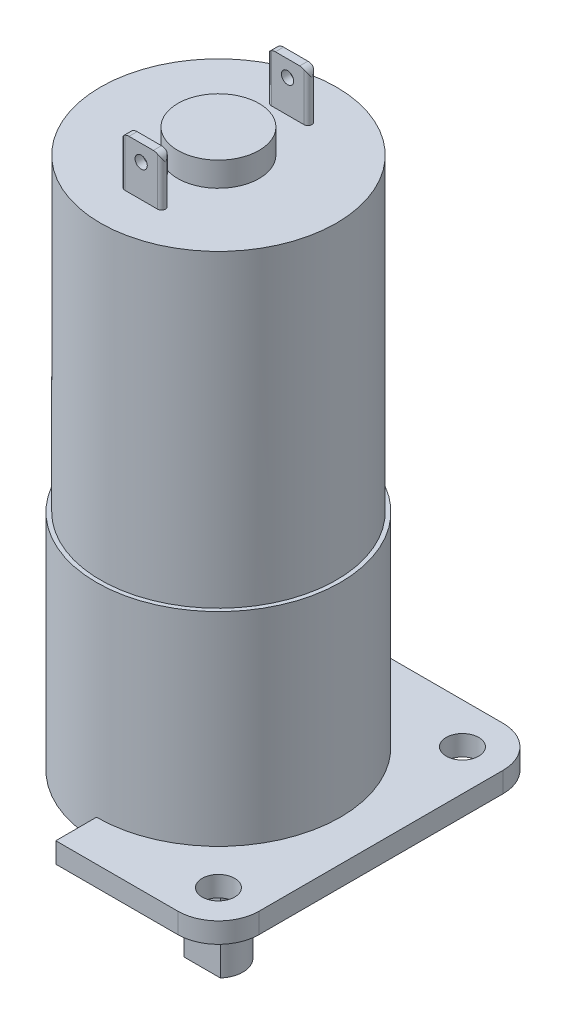
SolidWorks part; units mm, degrees
ref_plane "Alzado" through (0, 0, 0) normal (0, 0, 1) x (1, 0, 0)
ref_plane "Planta" through (0, 0, 0) normal (0, 1, 0) x (1, 0, 0)
ref_plane "Vista lateral" through (0, 0, 0) normal (1, 0, 0) x (0, 0, -1)
sketch "Croquis1" plane through (0, 0, 0) normal (0, 1, 0) x (1, 0, 0)
  circle A0 centre (0, 0) radius 14.5
  dimension "D1" = 29
extrude "Motor" add sketch "Croquis1" along normal blind 38
sketch "Croquis2" plane through (0, 38, 0) normal (0, 1, 0) x (1, 0, 0)
  circle A0 centre (0, 0) radius 5
  dimension "D1" = 10
extrude "Saliente posterior" add sketch "Croquis2" along normal blind 3
sketch "Croquis3" plane through (0, 38, 0) normal (0, 1, 0) x (1, 0, 0)
  line L0 (-11.3688, 9) -> (11.3688, 9) construction
  line L1 (-2, 9) -> (2, 9) construction
  line L2 (-2, 9.5) -> (2, 9.5)
  line L3 (-2, 8.5) -> (2, 8.5)
  line L4 (-14.5, 0) -> (14.5, 0) construction
  line L5 (-2, -9) -> (2, -9) construction
  line L6 (-2, -9.5) -> (2, -9.5)
  line L7 (-2, -8.5) -> (2, -8.5)
  circle A0 centre (0, 0) radius 14.5 construction
  arc A1 (-2, 9.5) -> (-2, 8.5) centre (-2, 9) ccw
  arc A2 (2, 8.5) -> (2, 9.5) centre (2, 9) ccw
  arc A3 (-2, -9.5) -> (-2, -8.5) centre (-2, -9) cw
  arc A4 (2, -8.5) -> (2, -9.5) centre (2, -9) cw
  point P7 (0, 9)
  point P17 (0, -9)
  dimension "D3" = 0.5
  dimension "D1" = 9
  dimension "D2" = 4
extrude "Bornes" add sketch "Croquis3" along normal blind 6
sketch "Croquis4" plane through (0, 0, 9.5) normal (0, 0, 1) x (1, 0, 0)
  line L0 (0, 44) -> (0, 38) construction
  line L1 (-2, 44) -> (2, 44) construction
  line L2 (-2, 38) -> (2, 38) construction
  line L3 (-2.5, 43) -> (2.5, 43) construction
  line L4 (-2.5, 44) -> (-2.5, 38) construction
  line L5 (2.5, 38) -> (2.5, 44) construction
  line L6 (-1.5, 44) -> (-1.5, 38) construction
  line L7 (14.5, 38) -> (-14.5, 38) construction
  line L8 (-2, 44) -> (-2.5, 44) construction
  line L9 (2.5, 43) -> (2.5, 44)
  line L10 (2.5, 44) -> (1.5, 44)
  line L11 (-2.5, 43) -> (-2.5, 44)
  line L12 (-2.5, 44) -> (-1.5, 44)
  arc A0 (-2.5, 43) -> (-1.5, 44) centre (-1.5, 43) cw
  arc A1 (2.5, 43) -> (1.5, 44) centre (1.5, 43) ccw
  circle A2 centre (0, 42) radius 0.75
  line M2 (2, 38) -> (2, 44)
  line M3 (2, 44) -> (-2, 44)
  line M4 (-2, 44) -> (-2, 38)
  dimension "D3" = 1.5
  dimension "D1" = 1
  dimension "D2" = 1
  dimension "D4" = 2
extrude "Agujero Bornes" cut sketch "Croquis4" against normal through all contours A2 | A1 L9 L10 M2 | A1 M2 M3 | L11 A0 L12 M4 | A0 M4 M3
sketch "Croquis5" plane through (0, 0, 0) normal (0, -1, 0) x (1, 0, 0)
  circle A0 centre (0, 0) radius 15
  dimension "D1" = 30
extrude "Caja reductora" add sketch "Croquis5" along normal blind 25
sketch "Croquis6" plane through (0, -25, 0) normal (0, -1, 0) x (1, 0, 0)
  line L1 (-15, 20) -> (15, 20)
  line L2 (-20, 15) -> (-20, -15)
  line L3 (-15, -20) -> (15, -20)
  line L4 (20, 15) -> (20, -15)
  line L5 (-20, 20) -> (20, -20) construction
  line L6 (-20, -20) -> (20, 20) construction
  circle A0 centre (-15, 15) radius 2
  circle A1 centre (15, 15) radius 2
  circle A2 centre (15, -15) radius 2
  circle A3 centre (-15, -15) radius 2
  arc A4 (-20, -15) -> (-15, -20) centre (-15, -15) ccw
  arc A5 (15, -20) -> (20, -15) centre (15, -15) ccw
  arc A6 (15, 20) -> (20, 15) centre (15, 15) cw
  arc A7 (-15, 20) -> (-20, 15) centre (-15, 15) ccw
  point P0 (0, 0)
  point P17 (0, 0)
  dimension "D3" = 4
  dimension "D6" = 5
  dimension "D1" = 40
  dimension "D2" = 40
  dimension "D4" = 5
  dimension "D5" = 4
extrude "Brida" add sketch "Croquis6" along normal blind 2.5
sketch "Croquis7" plane through (0, -27.5, 0) normal (0, -1, 0) x (1, 0, 0)
  circle A0 centre (0, 0) radius 6.5
  dimension "D1" = 13
extrude "Saliente eje" add sketch "Croquis7" along normal blind 3
sketch "Croquis8" plane through (0, -30.5, 0) normal (0, -1, 0) x (1, 0, 0)
  circle A0 centre (0, 0) radius 3
  dimension "D1" = 6
extrude "Eje" add sketch "Croquis8" along normal blind 17
sketch "Croquis9" plane through (0, -47.5, 0) normal (0, -1, 0) x (1, 0, 0)
  line L0 (-2.2361, 2) -> (2.2361, 2)
  circle A0 centre (0, 0) radius 3 construction
  circle A1 centre (0, 0) radius 3
  circle M1 centre (0, 0) radius 3
  dimension "D1" = 2
extrude "Corte Plano eje" cut sketch "Croquis9" against normal blind 10 contours L0 M1
sketch "Croquis10" plane through (0, -25, 0) normal (0, 1, 0) x (1, 0, 0)
  line L1 (-15, 20) -> (15, 20) construction
  line L2 (0, 20) -> (22.7102, 20)
  line L3 (0, 20) -> (0, -20.9832)
  line L4 (0, -20.9832) -> (22.7102, -20.9832)
  line L5 (22.7102, 20) -> (22.7102, -20.9832)
  circle A0 centre (0, 0) radius 15
  circle M2 centre (15, -15) radius 2
  line M4 (-20, 15) -> (-20, -15)
  arc M5 (-20, -15) -> (-15, -20) centre (-15, -15) ccw
  line M6 (-15, -20) -> (15, -20)
  arc M7 (15, -20) -> (20, -15) centre (15, -15) ccw
  line M8 (20, -15) -> (20, 15)
  circle M11 centre (-15, -15) radius 2
  circle M13 centre (0, 0) radius 15
extrude "Corte Brida" cut sketch "Croquis10" against normal blind 10 contours L2 M4 M5 M6 M7 M8 M13 M2 M11
